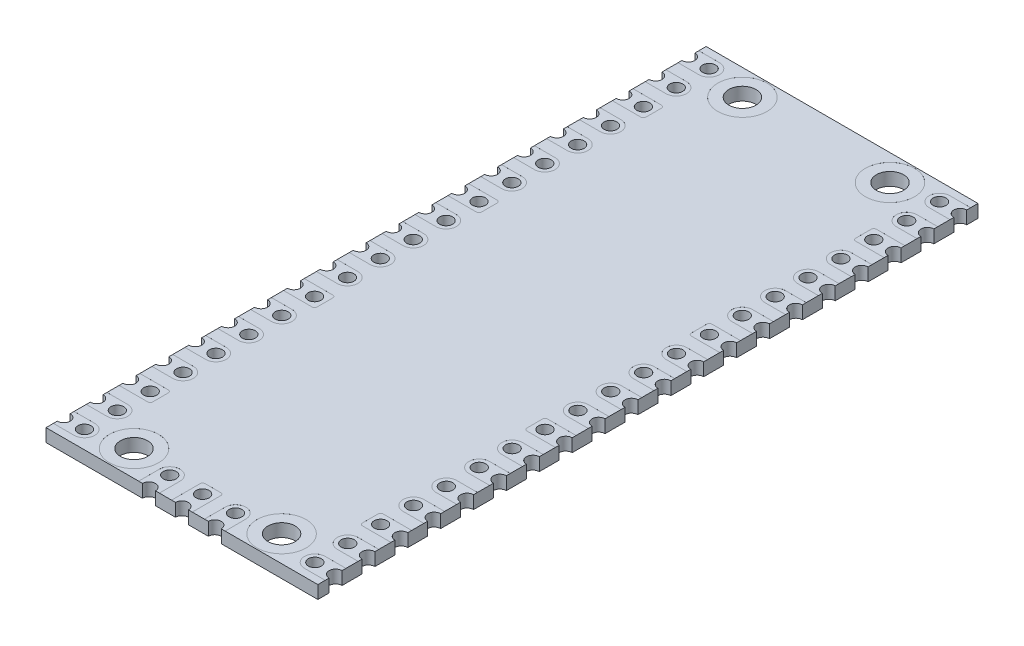
SolidWorks part; units mm, degrees
material "Power Circuit Board"
ref_plane "Front Plane" through (0, 0, 0) normal (0, 0, 1) x (1, 0, 0)
ref_plane "Top Plane" through (0, 0, 0) normal (0, 1, 0) x (1, 0, 0)
ref_plane "Right Plane" through (0, 0, 0) normal (1, 0, 0) x (0, 0, -1)
sketch "BaseS" plane through (0, 0, 0) normal (0, 1, 0) x (1, 0, 0)
  line L1 (-10.5, 25.5) -> (10.5, 25.5)
  line L2 (-10.5, 25.5) -> (-10.5, -25.5)
  line L3 (-10.5, -25.5) -> (10.5, -25.5)
  line L4 (10.5, 25.5) -> (10.5, -25.5)
  line L5 (-10.5, 25.5) -> (10.5, -25.5) construction
  line L6 (-10.5, -25.5) -> (10.5, 25.5) construction
  point P0 (0, 0)
  dimension "Width" = 21
  dimension "Length" = 51
extrude "Base" add sketch "BaseS" against normal mid plane 1
hole_wizard "Ø1.0 (1) Diameter Hole1" positions "Sketch2" profile "Sketch3" hole size "Ø1.0" standard "ANSI Metric" end condition through all
sketch "Sketch2" plane through (0, 0.5, 0) normal (0, 1, 0) x (1, 0, 0)
  line L0 (-10.5, 25.5) -> (-10.5, -25.5) construction
  line L1 (-10.5, -25.5) -> (10.5, -25.5) construction
  point P0 (-8.9, -24.13)
  dimension "XDim" = 1.6
  dimension "YDim" = 1.37
sketch "Sketch3" plane through (-8.9, 0.5, 24.13) normal (1, 0, 0) x (0, 0, 1)
  line L0 (0, 0) -> (0, 1)
  line L1 (0, 1) -> (0.5, 1)
  line L2 (0.5, 1) -> (0.5, 0)
  line L5 (0.5, 0) -> (0, 0)
  line L11 (0, -6.35) -> (0, 107.95) construction
  dimension "Thru Hole Dia." = 1
  dimension "Thru Hole Depth" = 1
pattern_linear "HoleHorzLP" count 2 spacing 1.6 along (1, 0, 0) of "Ø1.0 (1) Diameter Hole1"
sketch "SlotCutS" plane through (0, 0.5, 0) normal (0, 1, 0) x (1, 0, 0)
  line L0 (-8.9, -24.13) -> (-10.5, -24.13) construction
  line L1 (-8.9, -24.93) -> (-10.5, -24.93)
  line L2 (-8.9, -23.33) -> (-10.5, -23.33)
  arc A0 (-8.9, -24.93) -> (-8.9, -23.33) centre (-8.9, -24.13) ccw
  arc A1 (-10.5, -23.33) -> (-10.5, -24.93) centre (-10.5, -24.13) ccw
  circle A2 centre (-8.9, -24.13) radius 0.5 construction
  point P4 (-9.7, -24.13)
  dimension "RefDia" = 0.8
  dimension "DiaControl" = 0.3
extrude "SlotCut" cut sketch "SlotCutS" against normal blind 0.001
pattern_linear "HoleHorzLPSlotLP" count 20 spacing 2.54 along (0, 0, -1) of "Ø1.0 (1) Diameter Hole1", "HoleHorzLP", "SlotCut"
mirror "SHLPHM" about plane through (0, 0, 0) normal (1, 0, 0) of "Ø1.0 (1) Diameter Hole1", "HoleHorzLPSlotLP", "HoleHorzLP", "SlotCut"
hole_wizard "Ø2.1 (2.1) Diameter Hole1" positions "Sketch5" profile "Sketch6" hole size "Ø2.1" standard "ANSI Metric" end condition through all
sketch "Sketch5" plane through (0, 0.5, 0) normal (0, 1, 0) x (1, 0, 0)
  line L0 (-10.5, -25.5) -> (10.5, -25.5) construction
  line L1 (-10.5, -24.93) -> (-10.5, -25.5) construction
  point P0 (-5.7, -23.5)
  dimension "YDim" = 2
  dimension "XDim" = 4.8
sketch "Sketch6" plane through (-5.7, 0.5, 23.5) normal (1, 0, 0) x (0, 0, 1)
  line L0 (0, 0) -> (0, 1)
  line L1 (0, 1) -> (1.05, 1)
  line L2 (1.05, 1) -> (1.05, 0)
  line L5 (1.05, 0) -> (0, 0)
  line L11 (0, -6.35) -> (0, 107.95) construction
  dimension "Thru Hole Dia." = 2.1
  dimension "Thru Hole Depth" = 1
sketch "Soldering2.1mmHoleCutoutS" plane through (0, 0.5, 0) normal (0, 1, 0) x (1, 0, 0)
  circle A0 centre (-5.7, -23.5) radius 1.9
  circle A1 centre (-5.7, -23.5) radius 1.05 construction
  dimension "RefDia" = 3.8
  dimension "DiaControl" = 0.85
extrude "Soldering2.1mmHoleCutout" cut sketch "Soldering2.1mmHoleCutoutS" against normal up to surface (0.001 mm away) up to face at (-9.75, 0.499, 24.13)
mirror "SHCHM" about plane through (0, 0, 0) normal (1, 0, 0) of "Ø2.1 (2.1) Diameter Hole1", "Soldering2.1mmHoleCutout"
mirror "SHCHMVM" about plane through (0, 0, 0) normal (0, 0, 1) of "SHCHM", "Soldering2.1mmHoleCutout", "Ø2.1 (2.1) Diameter Hole1"
mirror "SHCTopVM" about plane through (0, 0, 0) normal (0, 1, 0) of "SHCHMVM", "SHCHM", "Soldering2.1mmHoleCutout"
sketch "SquareEtchS" plane through (0, 0.5, 0) normal (0, 1, 0) x (1, 0, 0)
  line L0 (-10.5, -19.85) -> (-10.5, -20.79) construction
  line L1 (-10.5, -18.25) -> (-8.3, -18.25)
  line L2 (-10.5, -18.25) -> (-10.5, -19.85)
  line L3 (-10.5, -19.85) -> (-8.3, -19.85)
  line L4 (-8.1, -18.45) -> (-8.1, -19.65)
  line L5 (-10.5, -19.85) -> (-8.9, -19.85) construction
  arc A0 (-8.9, -19.85) -> (-8.9, -18.25) centre (-8.9, -19.05) ccw construction
  arc A1 (-8.3, -19.85) -> (-8.1, -19.65) centre (-8.3, -19.65) ccw
  arc A2 (-8.1, -18.45) -> (-8.3, -18.25) centre (-8.3, -18.45) ccw
  dimension "Radius" = 0.2
extrude "SquareEtch" cut sketch "SquareEtchS" against normal up to surface (0.001 mm away) up to face at (-9.75, 0.499, 19.05)
pattern_linear "SELP" count 4 spacing 12.7 along (0, 0, 1) of "SquareEtch"
mirror "SELPHM" about plane through (0, 0, 0) normal (1, 0, 0) of "SELP", "SquareEtch"
hole_wizard "Ø1.0 (1) Diameter Hole2" positions "Sketch9" profile "Sketch10" hole size "Ø1.0" standard "ANSI Metric" end condition through all
sketch "Sketch9" plane through (0, 0.5, 0) normal (0, 1, 0) x (1, 0, 0)
  line L0 (0, -25.5) -> (0, -23.9) construction
  line L1 (-10.5, -25.5) -> (10.5, -25.5) construction
  point P0 (0, -23.9)
  dimension "YDim" = 1.6
sketch "Sketch10" plane through (0, 0.5, 23.9) normal (1, 0, 0) x (0, 0, 1)
  line L0 (0, 0) -> (0, 1)
  line L1 (0, 1) -> (0.5, 1)
  line L2 (0.5, 1) -> (0.5, 0)
  line L5 (0.5, 0) -> (0, 0)
  line L11 (0, -6.35) -> (0, 107.95) construction
  dimension "Thru Hole Dia." = 1
  dimension "Thru Hole Depth" = 1
sketch "VerticalSlotCutS" plane through (0, 0.5, 0) normal (0, 1, 0) x (1, 0, 0)
  line L0 (0, -23.9) -> (0, -25.5) construction
  line L1 (-10.5, -25.5) -> (10.5, -25.5) construction
  line L2 (0.8, -23.9) -> (0.8, -25.5)
  line L3 (-0.8, -23.9) -> (-0.8, -25.5)
  line L4 (-8.9, -24.13) -> (-10.5, -24.13) construction
  arc A0 (0.8, -23.9) -> (-0.8, -23.9) centre (0, -23.9) ccw
  arc A1 (-0.8, -25.5) -> (0.8, -25.5) centre (0, -25.5) ccw
  arc A2 (-8.9, -24.93) -> (-8.9, -23.33) centre (-8.9, -24.13) ccw construction
  point P4 (0, -24.7)
extrude "VerticalSlotCut" cut sketch "VerticalSlotCutS" against normal up to surface (0.999 mm away)
pattern_linear "DH2LP" count 2 spacing 1.6 along (0, 0, 1) of "Ø1.0 (1) Diameter Hole2"
pattern_linear "VSCHLP" count 2 spacing 2.54 along (1, 0, 0) count 2 spacing 2.54 along (-1, 0, 0) of "VerticalSlotCut", "Ø1.0 (1) Diameter Hole2", "DH2LP"
sketch "VerticalSquareEtchS" plane through (0, 0.5, 0) normal (0, 1, 0) x (1, 0, 0)
  line L0 (-1.74, -25.5) -> (-0.8, -25.5) construction
  line L1 (-0.6, -23.1) -> (0.6, -23.1)
  line L2 (-0.8, -23.3) -> (-0.8, -25.5)
  line L3 (-0.8, -25.5) -> (0.8, -25.5)
  line L4 (0.8, -23.3) -> (0.8, -25.5)
  line L5 (-0.8, -23.9) -> (-0.8, -25.5) construction
  arc A0 (0.8, -23.9) -> (-0.8, -23.9) centre (0, -23.9) ccw construction
  arc A1 (0.8, -23.3) -> (0.6, -23.1) centre (0.6, -23.3) ccw
  arc A2 (-0.6, -23.1) -> (-0.8, -23.3) centre (-0.6, -23.3) ccw
  arc A3 (-8.3, -19.85) -> (-8.1, -19.65) centre (-8.3, -19.65) ccw construction
extrude "VerticalSquareEtch" cut sketch "VerticalSquareEtchS" against normal up to surface (0.001 mm away)
sketch "VSCHPVMS" plane through (0, -0.5, 0) normal (0, -1, 0) x (1, 0, 0)
  line L0 (3.04, 25.5) -> (3.34, 25.5) construction
  line L1 (3.34, 25.5) -> (3.34, 23.9) construction
  line L2 (1.74, 23.9) -> (1.74, 25.5) construction
  line L3 (1.74, 25.5) -> (2.04, 25.5) construction
  line L4 (-2.04, 25.5) -> (-1.74, 25.5) construction
  line L5 (-1.74, 25.5) -> (-1.74, 23.9) construction
  line L6 (-3.34, 23.9) -> (-3.34, 25.5) construction
  line L7 (-3.34, 25.5) -> (-3.04, 25.5) construction
  line L8 (0.5, 25.5) -> (0.8, 25.5) construction
  line L9 (0.8, 25.5) -> (0.8, 23.3) construction
  line L10 (0.6, 23.1) -> (-0.6, 23.1) construction
  line L11 (-0.8, 23.3) -> (-0.8, 25.5) construction
  line L12 (-0.8, 25.5) -> (-0.5, 25.5) construction
  line L13 (3.04, 25.5) -> (3.34, 25.5)
  line L14 (3.34, 25.5) -> (3.34, 23.9)
  line L15 (1.74, 23.9) -> (1.74, 25.5)
  line L16 (1.74, 25.5) -> (2.04, 25.5)
  line L17 (-2.04, 25.5) -> (-1.74, 25.5)
  line L18 (-1.74, 25.5) -> (-1.74, 23.9)
  line L19 (-3.34, 23.9) -> (-3.34, 25.5)
  line L20 (-3.34, 25.5) -> (-3.04, 25.5)
  line L21 (0.5, 25.5) -> (0.8, 25.5)
  line L22 (0.8, 25.5) -> (0.8, 23.3)
  line L23 (0.6, 23.1) -> (-0.6, 23.1)
  line L24 (-0.8, 23.3) -> (-0.8, 25.5)
  line L25 (-0.8, 25.5) -> (-0.5, 25.5)
  arc A0 (2.04, 25.5) -> (3.04, 25.5) centre (2.54, 25.5) ccw construction
  arc A1 (1.74, 23.9) -> (3.34, 23.9) centre (2.54, 23.9) ccw construction
  arc A2 (-3.04, 25.5) -> (-2.04, 25.5) centre (-2.54, 25.5) ccw construction
  arc A3 (-3.34, 23.9) -> (-1.74, 23.9) centre (-2.54, 23.9) ccw construction
  arc A4 (-0.5, 25.5) -> (0.5, 25.5) centre (0, 25.5) ccw construction
  arc A5 (0.6, 23.1) -> (0.8, 23.3) centre (0.6, 23.3) ccw construction
  arc A6 (-0.8, 23.3) -> (-0.6, 23.1) centre (-0.6, 23.3) ccw construction
  arc A7 (2.04, 25.5) -> (3.04, 25.5) centre (2.54, 25.5) ccw
  arc A8 (1.74, 23.9) -> (3.34, 23.9) centre (2.54, 23.9) ccw
  arc A9 (-3.04, 25.5) -> (-2.04, 25.5) centre (-2.54, 25.5) ccw
  arc A10 (-3.34, 23.9) -> (-1.74, 23.9) centre (-2.54, 23.9) ccw
  arc A11 (-0.5, 25.5) -> (0.5, 25.5) centre (0, 25.5) ccw
  arc A12 (0.6, 23.1) -> (0.8, 23.3) centre (0.6, 23.3) ccw
  arc A13 (-0.8, 23.3) -> (-0.6, 23.1) centre (-0.6, 23.3) ccw
extrude "VSCHPVM" cut sketch "VSCHPVMS" against normal blind 0.001
equation "\"Depth@VSCHPVM\"=\"Depth@SlotCut\""
